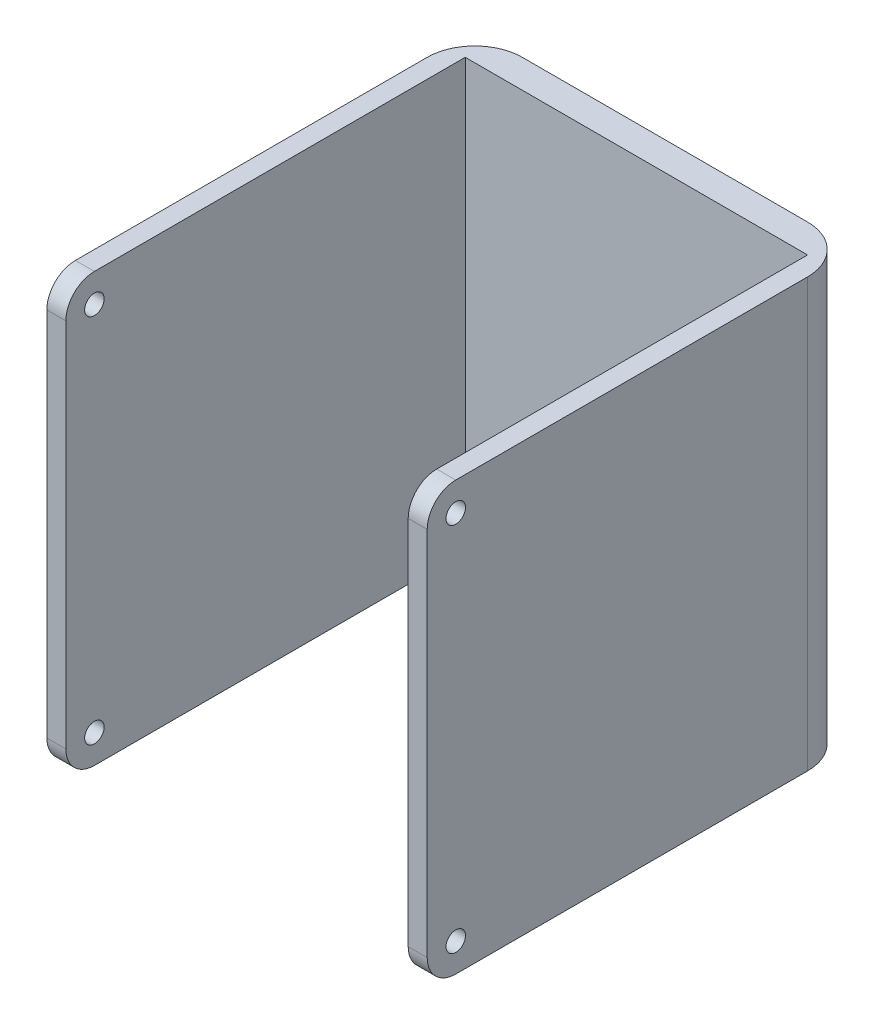
SolidWorks part; units mm, degrees
ref_plane "前基準面" through (0, 0, 0) normal (0, 0, 1) x (1, 0, 0)
ref_plane "上基準面" through (0, 0, 0) normal (0, 1, 0) x (1, 0, 0)
ref_plane "右基準面" through (0, 0, 0) normal (1, 0, 0) x (0, 0, -1)
sketch "草圖1" plane through (0, 0, 0) normal (0, 0, 1) x (1, 0, 0)
  line L1 (-14.5455, 16.9091) -> (25.4545, 16.9091)
  line L2 (-14.5455, 16.9091) -> (-14.5455, -28.0909)
  line L3 (-14.5455, -28.0909) -> (25.4545, -28.0909)
  line L4 (25.4545, 16.9091) -> (25.4545, -28.0909)
  dimension "D1" = 40
  dimension "D2" = 45
extrude "填料-伸長1" add sketch "草圖1" along normal blind 40 and the other way blind 5 contours L4 L3 L2 L1
sketch "草圖2" plane through (0, 16.9091, 0) normal (0, 1, 0) x (1, 0, 0)
  line L0 (5.4545, 5) -> (5.4545, -40.6532) construction
  line L1 (-14.5455, 5) -> (25.4545, 5) construction
  line L2 (-14.5455, -40) -> (25.4545, -40) construction
  line L3 (-12.5455, -3) -> (23.4545, -3)
  line L4 (-12.5455, -3) -> (-12.5455, -40)
  line L5 (-12.5455, -40) -> (23.4545, -40)
  line L6 (23.4545, -3) -> (23.4545, -40)
  line L7 (-14.5455, -40) -> (-14.5455, 5) construction
  line L8 (25.4545, -40) -> (25.4545, 5) construction
  dimension "D1" = 2
  dimension "D2" = 2
  dimension "D3" = 37
extrude "除料-伸長1" cut sketch "草圖2" against normal blind 50
sketch "草圖3" plane through (-14.5455, 0, 0) normal (-1, 0, 0) x (0, 0, 1)
  line L1 (40, -28.0909) -> (-5, -28.0909) construction
  line L2 (40, 16.9091) -> (40, -28.0909) construction
  line L3 (40, 16.9091) -> (-5, 16.9091) construction
  circle A1 centre (37, -25.0909) radius 1.025
  circle A2 centre (37, 13.9091) radius 1.025
  dimension "D5" = 3
  dimension "D6" = 2.05
  dimension "D1" = 2.05
  dimension "D2" = 3
  dimension "D3" = 3
  dimension "D4" = 3
extrude "除料-伸長2" cut sketch "草圖3" against normal blind 2
sketch "草圖4" plane through (25.4545, 0, 0) normal (1, 0, 0) x (0, 0, -1)
  line L0 (-40, 16.9091) -> (-40, -28.0909) construction
  line L1 (-40, -28.0909) -> (5, -28.0909) construction
  line L2 (-40, 16.9091) -> (5, 16.9091) construction
  circle A0 centre (-37, 13.9091) radius 1.025
  circle A1 centre (-37, -25.0909) radius 1.025
  dimension "D1" = 2.05
  dimension "D2" = 2.05
  dimension "D3" = 3
  dimension "D4" = 3
  dimension "D5" = 3
  dimension "D6" = 3
extrude "除料-伸長3" cut sketch "草圖4" against normal blind 2
sketch "草圖5" plane through (0, 16.9091, 0) normal (0, 1, 0) x (1, 0, 0)
  line L1 (-12.5455, -3) -> (23.4545, -3)
  line L2 (-12.5455, -3) -> (-12.5455, 2)
  line L3 (-12.5455, 2) -> (23.4545, 2)
  line L4 (23.4545, -3) -> (23.4545, 2)
  dimension "D1" = 36
  dimension "D2" = 5
extrude "除料-伸長4" cut sketch "草圖5" against normal blind 43
fillet "圓角6" radius 5 1 edges at (-14.5455, -5.5909, -5)
fillet "圓角7" radius 5 1 edges at (25.4545, -5.5909, -5)
fillet "圓角12" radius 3 1 edges at (-13.5455, -28.0909, 40)
fillet "圓角13" radius 3 1 edges at (24.4545, -28.0909, 40)
fillet "圓角14" radius 3 1 edges at (-13.5455, 16.9091, 40)
fillet "圓角15" radius 3 1 edges at (24.4545, 16.9091, 40)
